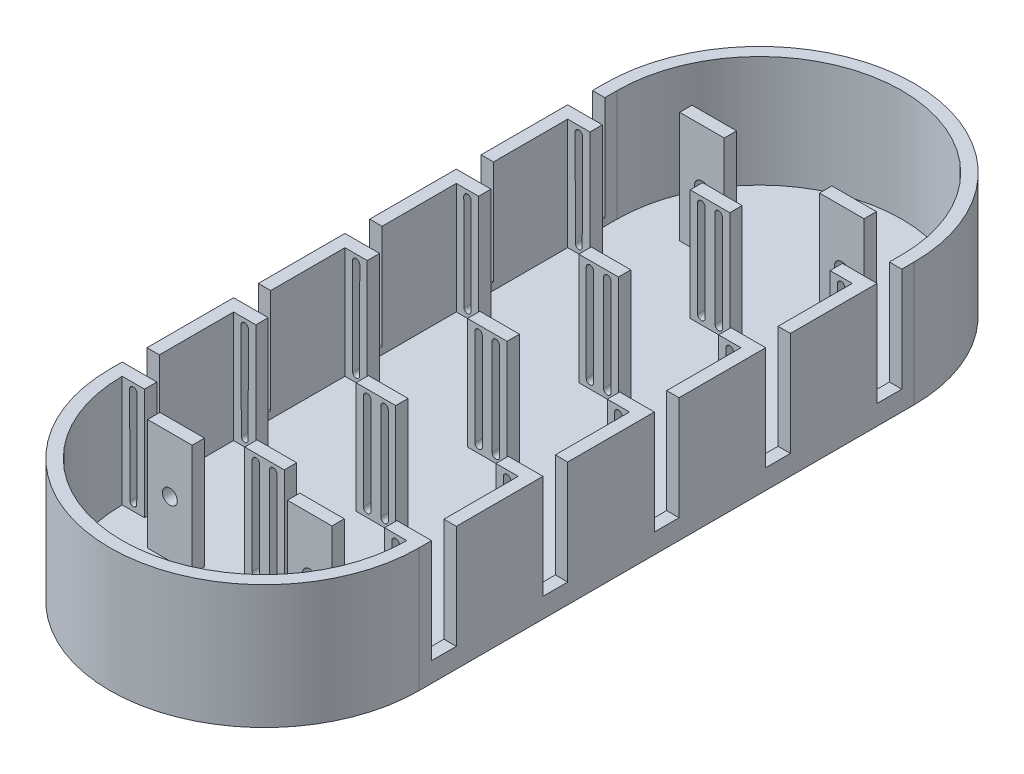
SolidWorks part; units mm, degrees
ref_plane "Front Plane" through (0, 0, 0) normal (0, 0, 1) x (1, 0, 0)
ref_plane "Top Plane" through (0, 0, 0) normal (0, 1, 0) x (1, 0, 0)
ref_plane "Right Plane" through (0, 0, 0) normal (1, 0, 0) x (0, 0, -1)
sketch "Sketch1" plane through (0, 0, 0) normal (0, 1, 0) x (1, 0, 0)
  line L0 (0, 0) -> (0, 200) construction
  line L1 (-62.5, 200) -> (-62.5, 0)
  line L2 (62.5, 0) -> (62.5, 200)
  arc A0 (-62.5, 0) -> (62.5, 0) centre (0, 0) ccw
  arc A1 (62.5, 200) -> (-62.5, 200) centre (0, 200) ccw
  dimension "D1" = 125
  dimension "D2" = 125
  dimension "D3" = 200
extrude "Boss-Extrude1" add sketch "Sketch1" along normal blind 5
sketch "Sketch2" plane through (0, 5, 0) normal (0, 1, 0) x (1, 0, 0)
  line L0 (-62.5, 200) -> (-62.5, 0)
  line L1 (62.5, 0) -> (62.5, 200)
  line L2 (-57.5, 200) -> (-57.5, 0)
  line L3 (57.5, 0) -> (57.5, 200)
  arc A0 (62.5, 200) -> (-62.5, 200) centre (0, 200) ccw
  arc A1 (-62.5, 0) -> (62.5, 0) centre (0, 0) ccw
  arc A2 (57.5, 200) -> (-57.5, 200) centre (0, 200) ccw
  arc A3 (-57.5, 0) -> (57.5, 0) centre (0, 0) ccw
  dimension "D1" = 5
sketch "Sketch3" plane through (0, 5, 0) normal (0, 1, 0) x (1, 0, 0)
  line L2 (0, 200) -> (0, 0)
  line L3 (-48.5, 5) -> (-8, 5)
  line L4 (-57.5, 0) -> (-48.5, 0)
  line L5 (-57.5, 0) -> (-57.5, 5)
  line L6 (-57.5, 5) -> (-48.5, 5)
  line L7 (-48.5, 0) -> (-48.5, 5)
  line L8 (-48.5, 5) -> (-48.5, 45) construction
  line L9 (-8, 5) -> (8, 5)
  line L10 (-8, 5) -> (-8, 0)
  line L11 (-8, 0) -> (8, 0)
  line L12 (0, 5) -> (0, 0)
  line L14 (-48.5, 45) -> (-57.5, 45)
  line L15 (-48.5, 45) -> (-48.5, 50)
  line L16 (-48.5, 50) -> (-57.5, 50)
  line L17 (-57.5, 45) -> (-57.5, 50)
  line L18 (-48.5, 50) -> (-48.5, 90) construction
  line L19 (-8, 50) -> (8, 50)
  line L20 (-8, 50) -> (-8, 45)
  line L21 (-8, 45) -> (8, 45)
  line L22 (0, 50) -> (0, 45)
  line L23 (-48.5, 95) -> (-48.5, 135) construction
  line L24 (-48.5, 90) -> (-57.5, 90)
  line L25 (-48.5, 90) -> (-48.5, 95)
  line L26 (-48.5, 95) -> (-57.5, 95)
  line L27 (-57.5, 90) -> (-57.5, 95)
  line L28 (-8, 95) -> (8, 95)
  line L29 (-8, 95) -> (-8, 90)
  line L30 (-8, 90) -> (8, 90)
  line L31 (0, 95) -> (0, 90)
  line L32 (-48.5, 140) -> (-48.5, 180) construction
  line L33 (-48.5, 135) -> (-57.5, 135)
  line L34 (-48.5, 135) -> (-48.5, 140)
  line L35 (-48.5, 140) -> (-57.5, 140)
  line L36 (-57.5, 135) -> (-57.5, 140)
  line L37 (-8, 135) -> (8, 135)
  line L38 (-8, 135) -> (-8, 140)
  line L39 (-8, 140) -> (8, 140)
  line L40 (0, 135) -> (0, 140)
  line L42 (-48.5, 180) -> (-57.5, 180)
  line L43 (-48.5, 180) -> (-48.5, 185)
  line L44 (-48.5, 185) -> (-57.5, 185)
  line L45 (-57.5, 180) -> (-57.5, 185)
  line L46 (8, 5) -> (8, 0)
  line L47 (-8, 180) -> (8, 180)
  line L48 (-8, 180) -> (-8, 185)
  line L49 (-8, 185) -> (8, 185)
  line L50 (0, 180) -> (0, 185)
  line L51 (57.5, 5) -> (48.5, 5)
  line L52 (48.5, 0) -> (48.5, 5)
  line L53 (57.5, 0) -> (48.5, 0)
  line L54 (57.5, 0) -> (57.5, 5)
  line L55 (8, 50) -> (8, 45)
  line L56 (48.5, 50) -> (57.5, 50)
  line L57 (57.5, 45) -> (57.5, 50)
  line L58 (48.5, 45) -> (57.5, 45)
  line L59 (48.5, 45) -> (48.5, 50)
  line L60 (48.5, 95) -> (57.5, 95)
  line L61 (57.5, 90) -> (57.5, 95)
  line L62 (48.5, 90) -> (57.5, 90)
  line L63 (48.5, 90) -> (48.5, 95)
  line L64 (8, 95) -> (8, 90)
  line L65 (8, 135) -> (8, 140)
  line L66 (48.5, 140) -> (57.5, 140)
  line L67 (57.5, 135) -> (57.5, 140)
  line L68 (48.5, 135) -> (57.5, 135)
  line L69 (48.5, 135) -> (48.5, 140)
  line L70 (8, 180) -> (8, 185)
  line L71 (48.5, 185) -> (57.5, 185)
  line L72 (57.5, 180) -> (57.5, 185)
  line L73 (48.5, 180) -> (57.5, 180)
  line L74 (48.5, 180) -> (48.5, 185)
  point P14 (0, 0)
  dimension "D1" = 200
  dimension "D2" = 9
  dimension "D3" = 8
  dimension "D4" = 8
  dimension "D5" = 40
  dimension "D6" = 5
  dimension "D7" = 5
  dimension "D8" = 40
  dimension "D9" = 5
  dimension "D10" = 8
  dimension "D11" = 8
  dimension "D12" = 40
  dimension "D13" = 5
  dimension "D14" = 5
  dimension "D15" = 40
  dimension "D16" = 8
extrude "Boss-Extrude3" add sketch "Sketch3" along normal blind 45
sketch "Sketch4" plane through (0, 0, 0) normal (0, 0, 1) x (1, 0, 0)
  line L0 (-53, 50) -> (-53, 5) construction
  line L1 (-57.5, 50) -> (-48.5, 50) construction
  line L2 (57.5, 5) -> (-57.5, 5) construction
  line L3 (-54.3698, 8) -> (-54.5, 47)
  line L4 (-51.5, 47) -> (-51.6302, 8)
  line L5 (-8, 50) -> (-3.5, 50) construction
  line L6 (-8, 50) -> (8, 50) construction
  line L7 (-3.5, 50) -> (-3.5, 5) construction
  line L8 (-5, 8) -> (-5, 47)
  line L9 (-2, 47) -> (-2, 8)
  line L10 (0, 50) -> (0, 5) construction
  line L11 (2, 47) -> (2, 8)
  line L12 (5, 8) -> (5, 47)
  line L13 (51.5, 47) -> (51.6302, 8)
  line L14 (54.3698, 8) -> (54.5, 47)
  arc A0 (-51.5, 47) -> (-54.5, 47) centre (-53, 47) ccw
  arc A1 (-54.3698, 8) -> (-51.6302, 8) centre (-53, 8) ccw
  arc A2 (-2, 47) -> (-5, 47) centre (-3.5, 47) ccw
  arc A3 (-5, 8) -> (-2, 8) centre (-3.5, 8) ccw
  arc A4 (5, 8) -> (2, 8) centre (3.5, 8) cw
  arc A5 (2, 47) -> (5, 47) centre (3.5, 47) cw
  arc A6 (54.3698, 8) -> (51.6302, 8) centre (53, 8) cw
  arc A7 (51.5, 47) -> (54.5, 47) centre (53, 47) cw
  dimension "D1" = 3
  dimension "D5" = 3
  dimension "D6" = 3
  dimension "D2" = 3
  dimension "D3" = 3
  dimension "D4" = 4.5
extrude "Cut-Extrude1" cut sketch "Sketch4" against normal blind 192
extrude "Boss-Extrude5" add sketch "Sketch2" along normal blind 45
sketch "Sketch5" plane through (-62.5, 0, 0) normal (-1, 0, 0) x (0, 0, 1)
  line L0 (0, 50) -> (-5, 50) construction
  line L1 (-200, 50) -> (0, 50) construction
  line L2 (-5, 50) -> (-15, 50)
  line L3 (-15, 50) -> (-50, 50) construction
  line L4 (-50, 50) -> (-60, 50)
  line L5 (-60, 50) -> (-95, 50) construction
  line L6 (-95, 50) -> (-105, 50)
  line L7 (-105, 50) -> (-140, 50) construction
  line L8 (-140, 50) -> (-150, 50)
  line L9 (-150, 50) -> (-185, 50) construction
  line L10 (-185, 50) -> (-195, 50)
  line L11 (-200, 0) -> (-200, 8) construction
  line L12 (-200, 50) -> (-200, 0) construction
  line L13 (-200, 8) -> (0, 8) construction
  line L14 (0, 50) -> (0, 0) construction
  line L16 (-195, 50) -> (-185, 50)
  line L17 (-195, 50) -> (-195, 8)
  line L18 (-195, 8) -> (-185, 8)
  line L19 (-185, 50) -> (-185, 8)
  line L20 (-150, 50) -> (-140, 50)
  line L21 (-150, 50) -> (-150, 8)
  line L22 (-150, 8) -> (-140, 8)
  line L23 (-140, 50) -> (-140, 8)
  line L24 (-105, 50) -> (-95, 50)
  line L25 (-105, 50) -> (-105, 8)
  line L26 (-105, 8) -> (-95, 8)
  line L27 (-95, 50) -> (-95, 8)
  line L28 (-60, 50) -> (-50, 50)
  line L29 (-60, 50) -> (-60, 8)
  line L30 (-60, 8) -> (-50, 8)
  line L31 (-50, 50) -> (-50, 8)
  line L32 (-15, 50) -> (-5, 50)
  line L33 (-15, 50) -> (-15, 8)
  line L34 (-15, 8) -> (-5, 8)
  line L35 (-5, 50) -> (-5, 8)
  line M15 (0, 50) -> (-200, 50)
  dimension "D1" = 5
  dimension "D2" = 10
  dimension "D3" = 35
  dimension "D4" = 10
  dimension "D5" = 35
  dimension "D6" = 10
  dimension "D7" = 35
  dimension "D8" = 10
  dimension "D9" = 35
  dimension "D10" = 10
  dimension "D11" = 8
extrude "Cut-Extrude2" cut sketch "Sketch5" against normal blind 129 contours L19 L17 L18 M15 | L23 L21 L22 M15 | L27 L25 L26 M15 | L31 L29 L30 M15 | L35 L33 L34 M15
sketch "Sketch6" plane through (0, 5, 0) normal (0, 1, 0) x (1, 0, 0)
  line L0 (-48.5, 185) -> (-8, 185) construction
  line L1 (-28.25, 185) -> (-28.25, 250.0818) construction
  line L2 (8, 185) -> (48.5, 185) construction
  line L3 (28.25, 185) -> (28.25, 250.0818) construction
  line L4 (-28.25, 205) -> (-37.25, 205)
  line L5 (-37.25, 205) -> (-37.25, 210)
  line L6 (-37.25, 210) -> (-19.25, 210)
  line L7 (-19.25, 210) -> (-19.25, 205)
  line L8 (-19.25, 205) -> (-28.25, 205)
  line L9 (28.25, 205) -> (19.25, 205)
  line L10 (19.25, 205) -> (19.25, 210)
  line L11 (19.25, 210) -> (37.25, 210)
  line L12 (37.25, 210) -> (37.25, 205)
  line L13 (37.25, 205) -> (28.25, 205)
  line L14 (0, 257.5) -> (0, -57.5) construction
  line L15 (-37.25, 100) -> (37.25, 100) construction
  line L16 (37.25, -10) -> (37.25, -5)
  line L17 (19.25, -10) -> (37.25, -10)
  line L18 (19.25, -5) -> (19.25, -10)
  line L19 (28.25, -5) -> (19.25, -5)
  line L20 (37.25, -5) -> (28.25, -5)
  line L21 (-19.25, -10) -> (-19.25, -5)
  line L22 (-37.25, -10) -> (-19.25, -10)
  line L23 (-37.25, -5) -> (-37.25, -10)
  line L24 (-28.25, -5) -> (-37.25, -5)
  line L25 (-19.25, -5) -> (-28.25, -5)
  arc A0 (57.5, 200) -> (-57.5, 200) centre (0, 200) ccw construction
  arc A1 (-57.5, 0) -> (57.5, 0) centre (0, 0) ccw construction
  dimension "D1" = 9
  dimension "D2" = 9
  dimension "D3" = 5
  dimension "D4" = 20
  dimension "D5" = 9
  dimension "D6" = 9
  dimension "D7" = 5
extrude "Boss-Extrude6" add sketch "Sketch6" along normal blind 45
sketch "Sketch7" plane through (0, 0, -205) normal (0, 0, 1) x (1, 0, 0)
  line L0 (-28.25, 50) -> (-28.25, 5) construction
  line L1 (-37.25, 50) -> (-19.25, 50) construction
  line L2 (-37.25, 5) -> (-19.25, 5) construction
  line L3 (-37.25, 27.5) -> (-19.25, 27.5) construction
  line L4 (-37.25, 50) -> (-37.25, 5) construction
  line L5 (-19.25, 50) -> (-19.25, 5) construction
  line L6 (28.25, 50) -> (28.25, 5) construction
  line L7 (19.25, 50) -> (37.25, 50) construction
  line L8 (19.25, 5) -> (37.25, 5) construction
  line L9 (19.25, 27.5) -> (37.25, 27.5) construction
  line L10 (19.25, 50) -> (19.25, 5) construction
  line L11 (37.25, 50) -> (37.25, 5) construction
  circle A0 centre (-28.25, 27.5) radius 3
  circle A1 centre (28.25, 27.5) radius 3
  dimension "D1" = 6
  dimension "D2" = 6
extrude "Cut-Extrude4" cut sketch "Sketch7" against normal blind 9 and the other way blind 224
